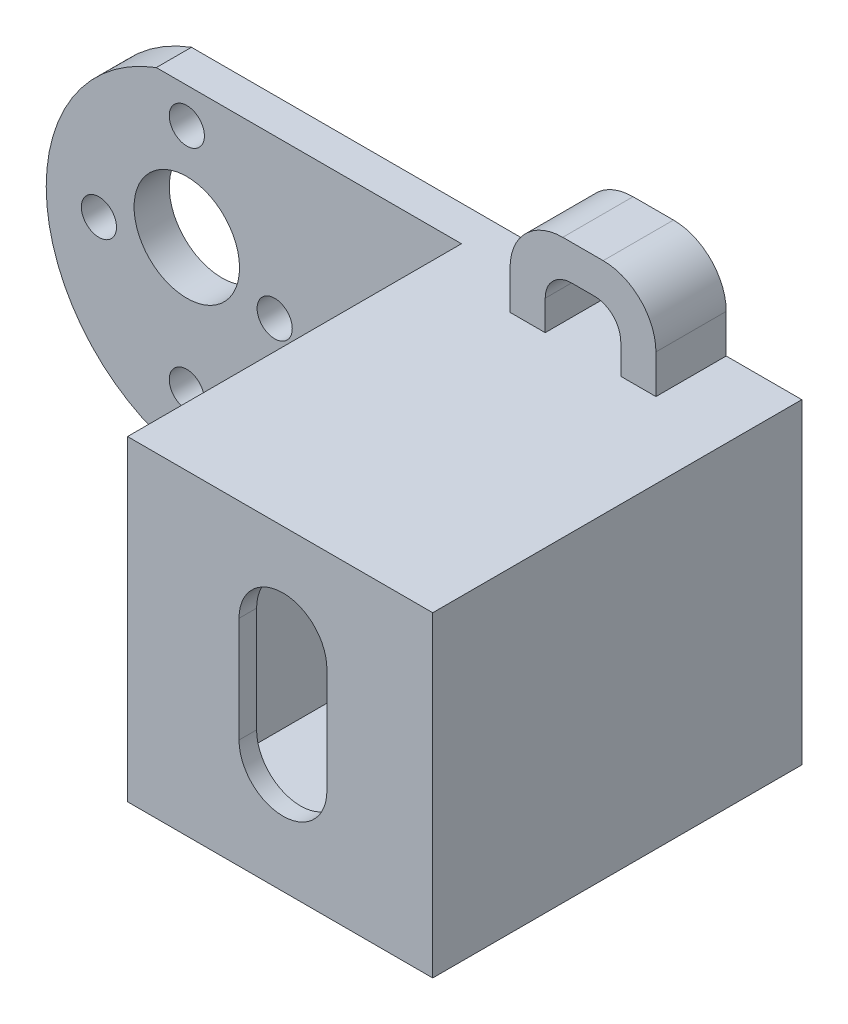
SolidWorks part; units mm, degrees
ref_plane "Front Plane" through (0, 0, 0) normal (0, 0, 1) x (1, 0, 0)
ref_plane "Top Plane" through (0, 0, 0) normal (0, 1, 0) x (1, 0, 0)
ref_plane "Right Plane" through (0, 0, 0) normal (1, 0, 0) x (0, 0, -1)
sketch "Sketch2" plane through (0, 0, 0) normal (0, 0, 1) x (1, 0, 0)
  line L0 (5.6806, 68.4289) -> (-42.0306, 68.4289) construction
  line L1 (-18.7355, 68.4289) -> (15.9929, 68.4289)
  line L2 (15.9929, 68.4289) -> (15.9929, 50.4289)
  line L3 (15.9929, 50.4289) -> (-18.7355, 50.4289)
  circle A0 centre (-17, 53.4289) radius 1
  circle A1 centre (-17, 60.9289) radius 3
  circle A2 centre (-22, 59.4289) radius 1
  circle A4 centre (-17, 66.4289) radius 1
  arc A5 (-18.7355, 68.4289) -> (-18.7355, 50.4289) centre (-15.4028, 59.4289) ccw
  circle A6 centre (-12, 59.4289) radius 1
  dimension "D1" = 2
  dimension "D2" = 2
  dimension "D3" = 2
  dimension "D4" = 2
extrude "Boss-Extrude2" add sketch "Sketch2" along normal blind 2
sketch "Sketch3" plane through (0, 0, 2) normal (0, 0, 1) x (1, 0, 0)
  line L0 (15.9929, 50.4289) -> (15.9929, 68.4289) construction
  line L1 (2.1929, 65.6789) -> (12.9929, 65.6789)
  line L2 (2.1929, 65.6789) -> (2.1929, 53.1789)
  line L3 (2.1929, 53.1789) -> (12.9929, 53.1789)
  line L4 (12.9929, 65.6789) -> (12.9929, 53.1789)
  line L5 (15.9929, 68.4289) -> (-18.7355, 68.4289) construction
  line L6 (-18.7355, 50.4289) -> (15.9929, 50.4289) construction
  dimension "D1" = 10.8
  dimension "D2" = 12.5
  dimension "D3" = 3
  dimension "D4" = 2.75
  dimension "D5" = 2.75
extrude "Cut-Extrude1" cut sketch "Sketch3" against normal through all
sketch "Sketch4" plane through (0, 0, 2) normal (0, 0, 1) x (1, 0, 0)
  line L0 (15.9929, 68.4289) -> (-18.7355, 68.4289) construction
  line L1 (-1.3713, 68.4289) -> (15.9929, 68.4289)
  line L2 (-1.3713, 68.4289) -> (-1.3713, 50.4289)
  line L3 (-1.3713, 50.4289) -> (15.9929, 50.4289)
  line L4 (15.9929, 68.4289) -> (15.9929, 50.4289)
extrude "Boss-Extrude3" add sketch "Sketch4" along normal blind 19
sketch "Sketch5" plane through (0, 0, 2) normal (0, 0, -1) x (-1, 0, 0)
  line L1 (-12.9929, 65.6789) -> (-2.1929, 65.6789)
  line L2 (-12.9929, 65.6789) -> (-12.9929, 53.1789)
  line L3 (-12.9929, 53.1789) -> (-2.1929, 53.1789)
  line L4 (-2.1929, 65.6789) -> (-2.1929, 53.1789)
extrude "Cut-Extrude2" cut sketch "Sketch5" against normal blind 18
sketch "Sketch7" plane through (0, 0, 0) normal (0, 0, -1) x (-1, 0, 0)
  line L0 (-15.9929, 68.4289) -> (18.7355, 68.4289) construction
  line L1 (-9.6929, 68.4289) -> (-5.3929, 68.4289)
  line L2 (-9.6929, 68.4289) -> (-9.6929, 71.6289)
  line L3 (-9.6929, 71.6289) -> (-5.3929, 71.6289)
  line L4 (-5.3929, 68.4289) -> (-5.3929, 71.6289)
  line L6 (-11.6929, 73.6289) -> (-3.3929, 73.6289)
  line L9 (-3.3929, 66.4289) -> (-3.3929, 73.6289) construction
  line L10 (-11.6929, 66.4289) -> (-3.3929, 66.4289) construction
  line L11 (-11.6929, 66.4289) -> (-11.6929, 73.6289) construction
  line L12 (-11.6929, 73.6289) -> (-11.6929, 68.4289)
  line L13 (-3.3929, 73.6289) -> (-3.3929, 68.4289)
  line L14 (-11.6929, 68.4289) -> (-9.6929, 68.4289)
  line L15 (-5.3929, 68.4289) -> (-3.3929, 68.4289)
  line M12 (18.7355, 68.4289) -> (-15.9929, 68.4289)
  dimension "D2" = 3.2
  dimension "D3" = 4.3
  dimension "D4" = 4.3
  dimension "D1" = 2
extrude "Boss-Extrude4" add sketch "Sketch7" against normal blind 4 contours L13 L6 L12 L2 L3 L4 M12
fillet "Fillet1" radius 1.5 2 edges at (5.3929, 71.6289, 2) (9.6929, 71.6289, 2)
fillet "Fillet2" radius 3 2 edges at (3.3929, 73.6289, 2) (11.6929, 73.6289, 2)
ref_plane "Plane1" through (0, 59.4289, 0) normal (0, 1, 0) x (1, 0, 0)
mirror "Mirror1" about plane through (0, 59.4289, 0) normal (0, 1, 0) of "Fillet2", "Fillet1", "Boss-Extrude4"
sketch "Sketch9" plane through (0, 0, 21) normal (0, 0, 1) x (1, 0, 0)
  line L0 (7.4715, 62.6449) -> (7.4715, 56.6449) construction
  line L1 (9.9715, 62.6449) -> (9.9715, 56.6449)
  line L2 (4.9715, 62.6449) -> (4.9715, 56.6449)
  arc A0 (9.9715, 62.6449) -> (4.9715, 62.6449) centre (7.4715, 62.6449) ccw
  arc A1 (4.9715, 56.6449) -> (9.9715, 56.6449) centre (7.4715, 56.6449) ccw
  point P2 (7.4715, 59.6449)
  dimension "D2" = 6
  dimension "D1" = 5
extrude "Cut-Extrude3" cut sketch "Sketch9" against normal blind 10
